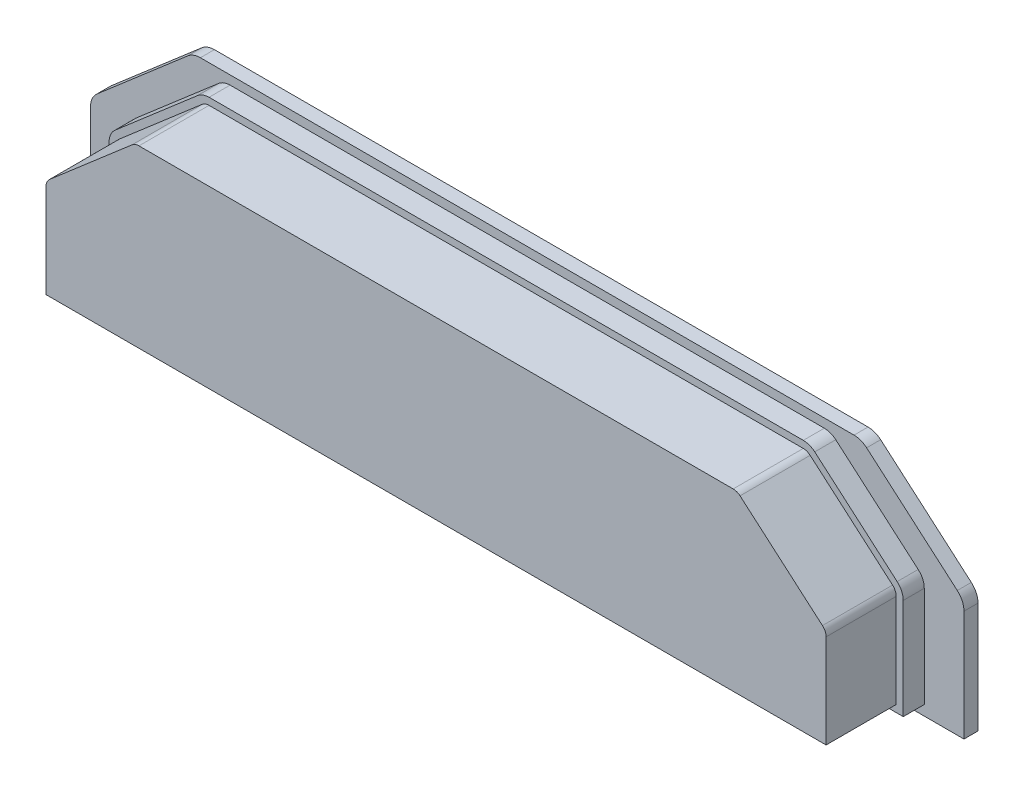
SolidWorks part; units mm, degrees
ref_plane "Front Plane" through (0, 0, 0) normal (0, 0, 1) x (1, 0, 0)
ref_plane "Top Plane" through (0, 0, 0) normal (0, 1, 0) x (1, 0, 0)
ref_plane "Right Plane" through (0, 0, 0) normal (1, 0, 0) x (0, 0, -1)
sketch "Sketch2" plane through (0, 3, 0) normal (0, 0, 1) x (1, 0, 0)
  line L2 (-56.625, -30) -> (56.625, -30)
  line L3 (56.625, -30) -> (56.625, -15.6446)
  line L4 (55.7585, -13.7521) -> (44.0052, -3.6075)
  line L5 (42.3717, -3) -> (-42.3717, -3)
  line L6 (-44.0052, -3.6075) -> (-55.7585, -13.7521)
  line L7 (-56.625, -15.6446) -> (-56.625, -30)
  arc A0 (56.625, -15.6446) -> (55.7585, -13.7521) centre (54.125, -15.6446) ccw
  arc A1 (44.0052, -3.6075) -> (42.3717, -3) centre (42.3717, -5.5) ccw
  arc A2 (-55.7585, -13.7521) -> (-56.625, -15.6446) centre (-54.125, -15.6446) ccw
  arc A3 (-42.3717, -3) -> (-44.0052, -3.6075) centre (-42.3717, -5.5) ccw
  point P0 (0, -3)
  point P8 (0, -30)
  point P15 (56.625, -14.5)
  point P18 (43.3014, -3)
  point P23 (-43.3014, -3)
  dimension "D6" = 2.5
  dimension "D1" = 113.25
  dimension "D2" = 15.5
  dimension "D3" = 27
  dimension "D4" = 86.6028
extrude "Boss-Extrude1" add sketch "Sketch2" along normal blind 3
sketch "Sketch5" plane through (0, 0, 3) normal (0, 0, 1) x (1, 0, 0)
  line L12 (55.625, -26) -> (55.625, -12.6446)
  line L13 (55.1051, -11.5091) -> (43.3518, -1.3645)
  line L14 (42.3717, -1) -> (-42.3717, -1)
  line L15 (-43.3518, -1.3645) -> (-55.1051, -11.5091)
  line L16 (-55.625, -12.6446) -> (-55.625, -26)
  line L17 (-55.625, -26) -> (55.625, -26)
  line L18 (55.625, -26) -> (55.625, -12.6446)
  line L19 (55.1051, -11.5091) -> (43.3518, -1.3645)
  line L20 (42.3717, -1) -> (-42.3717, -1)
  line L21 (-43.3518, -1.3645) -> (-55.1051, -11.5091)
  line L22 (-55.625, -12.6446) -> (-55.625, -26)
  line L23 (-55.625, -26) -> (55.625, -26)
  arc A8 (55.625, -12.6446) -> (55.1051, -11.5091) centre (54.125, -12.6446) ccw
  arc A9 (43.3518, -1.3645) -> (42.3717, -1) centre (42.3717, -2.5) ccw
  arc A10 (-42.3717, -1) -> (-43.3518, -1.3645) centre (-42.3717, -2.5) ccw
  arc A11 (-55.1051, -11.5091) -> (-55.625, -12.6446) centre (-54.125, -12.6446) ccw
  arc A12 (55.625, -12.6446) -> (55.1051, -11.5091) centre (54.125, -12.6446) ccw
  arc A13 (43.3518, -1.3645) -> (42.3717, -1) centre (42.3717, -2.5) ccw
  arc A14 (-42.3717, -1) -> (-43.3518, -1.3645) centre (-42.3717, -2.5) ccw
  arc A15 (-55.1051, -11.5091) -> (-55.625, -12.6446) centre (-54.125, -12.6446) ccw
  dimension "D1" = 1
extrude "Boss-Extrude4" add sketch "Sketch5" along normal blind 10
sketch "Sketch6" plane through (0, 0, 0) normal (0, 0, -1) x (-1, 0, 0)
  line L12 (-62.2875, -12.6446) -> (-62.2875, -28.4355)
  line L13 (-62.2875, -28.4355) -> (62.2875, -28.4355)
  line L14 (62.2875, -28.4355) -> (62.2875, -12.6446)
  line L15 (61.3344, -10.5628) -> (48.4057, 0.5962)
  line L16 (46.6089, 1.2645) -> (-46.6089, 1.2645)
  line L17 (-48.4057, 0.5962) -> (-61.3344, -10.5628)
  arc A8 (62.2875, -12.6446) -> (61.3344, -10.5628) centre (59.5375, -12.6446) ccw
  arc A9 (48.4057, 0.5962) -> (46.6089, 1.2645) centre (46.6089, -1.4855) ccw
  arc A10 (-46.6089, 1.2645) -> (-48.4057, 0.5962) centre (-46.6089, -1.4855) ccw
  arc A11 (-61.3344, -10.5628) -> (-62.2875, -12.6446) centre (-59.5375, -12.6446) ccw
extrude "Boss-Extrude5" add sketch "Sketch6" along normal blind 2
